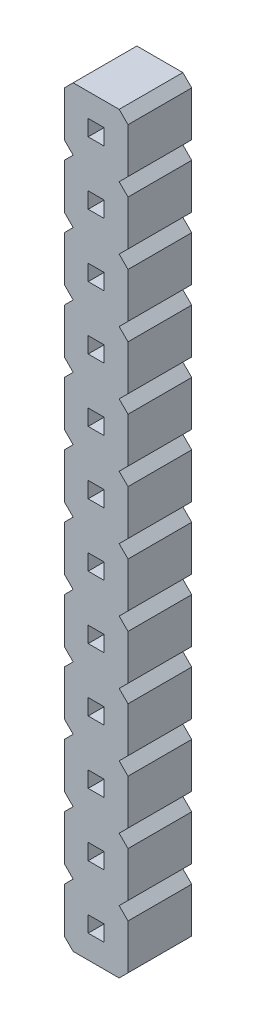
SolidWorks part; units mm, degrees
ref_plane "Alzado" through (0, 0, 0) normal (0, 0, 1) x (1, 0, 0)
ref_plane "Planta" through (0, 0, 0) normal (0, 1, 0) x (1, 0, 0)
ref_plane "Vista lateral" through (0, 0, 0) normal (1, 0, 0) x (0, 0, -1)
sketch "pin_drawing" plane through (0, 0, 0) normal (0, 0, 1) x (1, 0, 0)
  line L0 (0.9525, -0.932) -> (0, -0.932) construction
  line L1 (0, 2.1464) -> (0, 0.3536)
  line L2 (0, -0.3536) -> (0, -2.1464)
  line L3 (0, -0.3536) -> (0.3536, 0)
  line L4 (1.5885, -1.568) -> (2.541, -1.568) construction
  line L5 (0, 2.1464) -> (0.3536, 2.5)
  line L6 (2.541, -0.3536) -> (2.541, -2.1464)
  line L7 (0.9525, -1.25) -> (0.9525, -0.932) construction
  line L8 (2.541, -2.1464) -> (2.1874, -2.5)
  line L9 (2.1874, 0) -> (2.541, -0.3536)
  line L10 (1.5885, -1.25) -> (1.5885, -1.568) construction
  line L11 (0.3536, -2.5) -> (0, -2.1464)
  line L12 (0.9525, -0.932) -> (1.5885, -0.932)
  line L13 (0.9525, -0.932) -> (0.9525, -1.568)
  line L14 (0.9525, -1.568) -> (1.5885, -1.568)
  line L15 (1.5885, -0.932) -> (1.5885, -1.568)
  line L16 (2.541, 2.1464) -> (2.541, 0.3536)
  line L17 (2.541, 0.3536) -> (2.1874, 0)
  line L18 (2.1874, 2.5) -> (2.541, 2.1464)
  line L19 (0.3536, 0) -> (0, 0.3536)
  line L20 (0.9525, 1.568) -> (1.5885, 1.568)
  line L21 (0.9525, 1.568) -> (0.9525, 0.932)
  line L22 (0.9525, 0.932) -> (1.5885, 0.932)
  line L23 (1.5885, 1.568) -> (1.5885, 0.932)
  line L24 (0.9525, 1.568) -> (0, 1.568) construction
  line L25 (1.5885, 0.932) -> (2.541, 0.932) construction
  line L26 (0.9525, 1.25) -> (0.9525, 1.568) construction
  line L27 (1.5885, 1.25) -> (1.5885, 0.932) construction
  line L28 (0, 4.6464) -> (0, 2.8536)
  line L29 (0, 4.6464) -> (0.3536, 5)
  line L30 (2.541, 4.6464) -> (2.541, 2.8536)
  line L31 (2.541, 2.8536) -> (2.1874, 2.5)
  line L32 (2.1874, 5) -> (2.541, 4.6464)
  line L33 (0.3536, 2.5) -> (0, 2.8536)
  line L34 (0.9525, 4.068) -> (1.5885, 4.068)
  line L35 (0.9525, 4.068) -> (0.9525, 3.432)
  line L36 (0.9525, 3.432) -> (1.5885, 3.432)
  line L37 (1.5885, 4.068) -> (1.5885, 3.432)
  line L38 (0.9525, 4.068) -> (0, 4.068) construction
  line L39 (1.5885, 3.432) -> (2.541, 3.432) construction
  line L40 (0.9525, 3.75) -> (0.9525, 4.068) construction
  line L41 (1.5885, 3.75) -> (1.5885, 3.432) construction
  line L42 (0, 7.1464) -> (0, 5.3536)
  line L43 (0, 7.1464) -> (0.3536, 7.5)
  line L44 (2.541, 7.1464) -> (2.541, 5.3536)
  line L45 (2.541, 5.3536) -> (2.1874, 5)
  line L46 (2.1874, 7.5) -> (2.541, 7.1464)
  line L47 (0.3536, 5) -> (0, 5.3536)
  line L48 (0.9525, 6.568) -> (1.5885, 6.568)
  line L49 (0.9525, 6.568) -> (0.9525, 5.932)
  line L50 (0.9525, 5.932) -> (1.5885, 5.932)
  line L51 (1.5885, 6.568) -> (1.5885, 5.932)
  line L52 (0.9525, 6.568) -> (0, 6.568) construction
  line L53 (1.5885, 5.932) -> (2.541, 5.932) construction
  line L54 (0.9525, 6.25) -> (0.9525, 6.568) construction
  line L55 (1.5885, 6.25) -> (1.5885, 5.932) construction
  line L56 (0, 9.6464) -> (0, 7.8536)
  line L57 (0, 9.6464) -> (0.3536, 10)
  line L58 (2.541, 9.6464) -> (2.541, 7.8536)
  line L59 (2.541, 7.8536) -> (2.1874, 7.5)
  line L60 (2.1874, 10) -> (2.541, 9.6464)
  line L61 (0.3536, 7.5) -> (0, 7.8536)
  line L62 (0.9525, 9.068) -> (1.5885, 9.068)
  line L63 (0.9525, 9.068) -> (0.9525, 8.432)
  line L64 (0.9525, 8.432) -> (1.5885, 8.432)
  line L65 (1.5885, 9.068) -> (1.5885, 8.432)
  line L66 (0.9525, 9.068) -> (0, 9.068) construction
  line L67 (1.5885, 8.432) -> (2.541, 8.432) construction
  line L68 (0.9525, 8.75) -> (0.9525, 9.068) construction
  line L69 (1.5885, 8.75) -> (1.5885, 8.432) construction
  line L70 (0, 12.1464) -> (0, 10.3536)
  line L71 (0, 12.1464) -> (0.3536, 12.5)
  line L72 (2.541, 12.1464) -> (2.541, 10.3536)
  line L73 (2.541, 10.3536) -> (2.1874, 10)
  line L74 (2.1874, 12.5) -> (2.541, 12.1464)
  line L75 (0.3536, 10) -> (0, 10.3536)
  line L76 (0.9525, 11.568) -> (1.5885, 11.568)
  line L77 (0.9525, 11.568) -> (0.9525, 10.932)
  line L78 (0.9525, 10.932) -> (1.5885, 10.932)
  line L79 (1.5885, 11.568) -> (1.5885, 10.932)
  line L80 (0.9525, 11.568) -> (0, 11.568) construction
  line L81 (1.5885, 10.932) -> (2.541, 10.932) construction
  line L82 (0.9525, 11.25) -> (0.9525, 11.568) construction
  line L83 (1.5885, 11.25) -> (1.5885, 10.932) construction
  line L84 (0, 14.6464) -> (0, 12.8536)
  line L85 (0, 14.6464) -> (0.3536, 15)
  line L86 (2.541, 14.6464) -> (2.541, 12.8536)
  line L87 (2.541, 12.8536) -> (2.1874, 12.5)
  line L88 (2.1874, 15) -> (2.541, 14.6464)
  line L89 (0.3536, 12.5) -> (0, 12.8536)
  line L90 (0.9525, 14.068) -> (1.5885, 14.068)
  line L91 (0.9525, 14.068) -> (0.9525, 13.432)
  line L92 (0.9525, 13.432) -> (1.5885, 13.432)
  line L93 (1.5885, 14.068) -> (1.5885, 13.432)
  line L94 (0.9525, 14.068) -> (0, 14.068) construction
  line L95 (1.5885, 13.432) -> (2.541, 13.432) construction
  line L96 (0.9525, 13.75) -> (0.9525, 14.068) construction
  line L97 (1.5885, 13.75) -> (1.5885, 13.432) construction
  line L98 (0, 17.1464) -> (0, 15.3536)
  line L99 (0, 17.1464) -> (0.3536, 17.5)
  line L100 (2.541, 17.1464) -> (2.541, 15.3536)
  line L101 (2.541, 15.3536) -> (2.1874, 15)
  line L102 (2.1874, 17.5) -> (2.541, 17.1464)
  line L103 (0.3536, 15) -> (0, 15.3536)
  line L104 (0.9525, 16.568) -> (1.5885, 16.568)
  line L105 (0.9525, 16.568) -> (0.9525, 15.932)
  line L106 (0.9525, 15.932) -> (1.5885, 15.932)
  line L107 (1.5885, 16.568) -> (1.5885, 15.932)
  line L108 (0.9525, 16.568) -> (0, 16.568) construction
  line L109 (1.5885, 15.932) -> (2.541, 15.932) construction
  line L110 (0.9525, 16.25) -> (0.9525, 16.568) construction
  line L111 (1.5885, 16.25) -> (1.5885, 15.932) construction
  line L112 (0, 19.6464) -> (0, 17.8536)
  line L113 (0, 19.6464) -> (0.3536, 20)
  line L114 (2.541, 19.6464) -> (2.541, 17.8536)
  line L115 (2.541, 17.8536) -> (2.1874, 17.5)
  line L116 (2.1874, 20) -> (2.541, 19.6464)
  line L117 (0.3536, 17.5) -> (0, 17.8536)
  line L118 (0.9525, 19.068) -> (1.5885, 19.068)
  line L119 (0.9525, 19.068) -> (0.9525, 18.432)
  line L120 (0.9525, 18.432) -> (1.5885, 18.432)
  line L121 (1.5885, 19.068) -> (1.5885, 18.432)
  line L122 (0.9525, 19.068) -> (0, 19.068) construction
  line L123 (1.5885, 18.432) -> (2.541, 18.432) construction
  line L124 (0.9525, 18.75) -> (0.9525, 19.068) construction
  line L125 (1.5885, 18.75) -> (1.5885, 18.432) construction
  line L126 (0, 22.1464) -> (0, 20.3536)
  line L127 (0, 22.1464) -> (0.3536, 22.5)
  line L128 (2.541, 22.1464) -> (2.541, 20.3536)
  line L129 (2.541, 20.3536) -> (2.1874, 20)
  line L130 (2.1874, 22.5) -> (2.541, 22.1464)
  line L131 (0.3536, 20) -> (0, 20.3536)
  line L132 (0.9525, 21.568) -> (1.5885, 21.568)
  line L133 (0.9525, 21.568) -> (0.9525, 20.932)
  line L134 (0.9525, 20.932) -> (1.5885, 20.932)
  line L135 (1.5885, 21.568) -> (1.5885, 20.932)
  line L136 (0.9525, 21.568) -> (0, 21.568) construction
  line L137 (1.5885, 20.932) -> (2.541, 20.932) construction
  line L138 (0.9525, 21.25) -> (0.9525, 21.568) construction
  line L139 (1.5885, 21.25) -> (1.5885, 20.932) construction
  line L140 (0, 24.6464) -> (0, 22.8536)
  line L141 (0, 24.6464) -> (0.3536, 25)
  line L142 (2.541, 24.6464) -> (2.541, 22.8536)
  line L143 (2.541, 22.8536) -> (2.1874, 22.5)
  line L144 (2.1874, 25) -> (2.541, 24.6464)
  line L145 (0.3536, 22.5) -> (0, 22.8536)
  line L146 (0.9525, 24.068) -> (1.5885, 24.068)
  line L147 (0.9525, 24.068) -> (0.9525, 23.432)
  line L148 (0.9525, 23.432) -> (1.5885, 23.432)
  line L149 (1.5885, 24.068) -> (1.5885, 23.432)
  line L150 (0.9525, 24.068) -> (0, 24.068) construction
  line L151 (1.5885, 23.432) -> (2.541, 23.432) construction
  line L152 (0.9525, 23.75) -> (0.9525, 24.068) construction
  line L153 (1.5885, 23.75) -> (1.5885, 23.432) construction
  line L154 (0, 27.1464) -> (0, 25.3536)
  line L155 (0, 27.1464) -> (0.3536, 27.5)
  line L156 (2.541, 27.1464) -> (2.541, 25.3536)
  line L157 (2.541, 25.3536) -> (2.1874, 25)
  line L158 (2.1874, 27.5) -> (2.541, 27.1464)
  line L159 (0.3536, 25) -> (0, 25.3536)
  line L160 (0.9525, 26.568) -> (1.5885, 26.568)
  line L161 (0.9525, 26.568) -> (0.9525, 25.932)
  line L162 (0.9525, 25.932) -> (1.5885, 25.932)
  line L163 (1.5885, 26.568) -> (1.5885, 25.932)
  line L164 (0.9525, 26.568) -> (0, 26.568) construction
  line L165 (1.5885, 25.932) -> (2.541, 25.932) construction
  line L166 (0.9525, 26.25) -> (0.9525, 26.568) construction
  line L167 (1.5885, 26.25) -> (1.5885, 25.932) construction
  line L168 (2.1874, -2.5) -> (0.3536, -2.5)
  line L169 (0.3536, 27.5) -> (2.1874, 27.5)
  dimension "D1" = 0.318
  dimension "D2" = 0.9525
  dimension "D3" = 0.5
  dimension "D4" = 135
  dimension "D5" = 0.5
  dimension "D6" = 135
  dimension "D7" = 12
extrude "Boss-Extrude1" add sketch "pin_drawing" along normal blind 2.54
